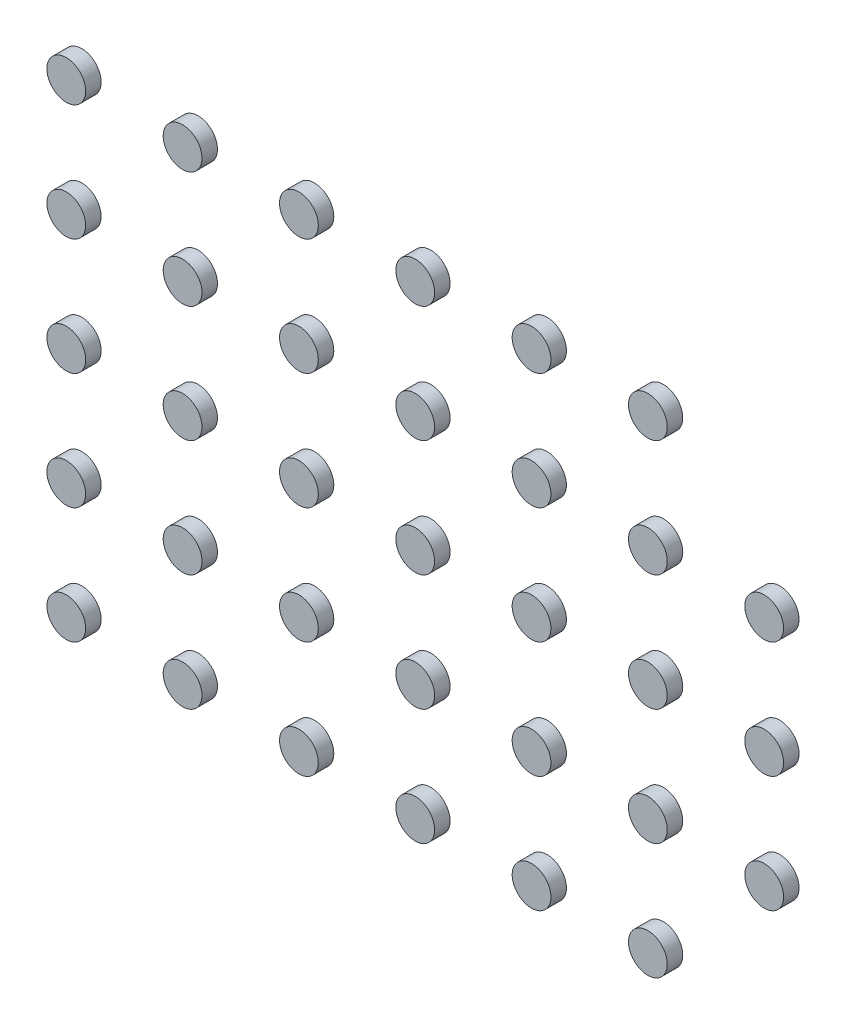
SolidWorks part; units mm, degrees
ref_plane "前视基准面" through (0, 0, 0) normal (0, 0, 1) x (1, 0, 0)
ref_plane "上视基准面" through (0, 0, 0) normal (0, 1, 0) x (1, 0, 0)
ref_plane "右视基准面" through (0, 0, 0) normal (1, 0, 0) x (0, 0, -1)
other "Configuration Table"
sketch "草图1" plane through (0, 0, 0) normal (0, 0, 1) x (1, 0, 0)
  circle A0 centre (-10.5, -7.5) radius 0.5
  circle A1 centre (-10.5, -4.5) radius 0.5
  circle A2 centre (-10.5, -1.5) radius 0.5
  circle A3 centre (-10.5, 4.5) radius 0.5
  circle A4 centre (-7.5, 4.5) radius 0.5
  circle A5 centre (-7.5, -1.5) radius 0.5
  circle A6 centre (-7.5, -4.5) radius 0.5
  circle A7 centre (-7.5, -7.5) radius 0.5
  circle A8 centre (-4.5, -7.5) radius 0.5
  circle A9 centre (-4.5, -4.5) radius 0.5
  circle A10 centre (-4.5, 1.5) radius 0.5
  circle A11 centre (-4.5, 4.5) radius 0.5
  circle A12 centre (-1.5, 4.5) radius 0.5
  circle A13 centre (-1.5, 1.5) radius 0.5
  circle A14 centre (1.5, -1.5) radius 0.5
  circle A15 centre (-1.5, -1.5) radius 0.5
  circle A16 centre (-1.5, -4.5) radius 0.5
  circle A17 centre (-1.5, -7.5) radius 0.5
  circle A18 centre (1.5, -7.5) radius 0.5
  circle A19 centre (1.5, -4.5) radius 0.5
  circle A20 centre (1.5, 1.5) radius 0.5
  circle A21 centre (1.5, 4.5) radius 0.5
  circle A22 centre (4.5, 4.5) radius 0.5
  circle A23 centre (4.5, 1.5) radius 0.5
  circle A24 centre (4.5, -1.5) radius 0.5
  circle A25 centre (4.5, -4.5) radius 0.5
  circle A26 centre (4.5, -7.5) radius 0.5
  circle A27 centre (7.5, -4.5) radius 0.5
  circle A28 centre (7.5, 1.5) radius 0.5
  circle A29 centre (7.5, -1.5) radius 0.5
  circle A30 centre (10.5, -1.5) radius 0.5
  circle A31 centre (10.5, 1.5) radius 0.5
  circle A32 centre (7.5, 4.5) radius 0.5
  circle A33 centre (4.5, 7.5) radius 0.5
  circle A34 centre (1.5, 7.5) radius 0.5
  circle A35 centre (-1.5, 7.5) radius 0.5
  circle A36 centre (-4.5, 7.5) radius 0.5
  circle A37 centre (-7.5, 7.5) radius 0.5
  circle A38 centre (-10.5, 7.5) radius 0.5
  circle A39 centre (-4.5, -1.5) radius 0.5
  circle A40 centre (-1.5, -1.5) radius 0.5
  circle A41 centre (-7.5, 1.5) radius 0.5
  circle A42 centre (-10.5, 1.5) radius 0.5
extrude "凸台-拉伸1" add sketch "草图1" along normal blind 0.4 contours A10 | A13 | A20 | A23 | A28 | A31 | A30 | A29 | A38 | A35 | A34 | A33 | A42 | A3 | A2 | A1 | A0 | A7 | A6 | A5 | A41 | A4 | A11 | A12 | A21 | A32 | A14 | A15 | A39 | A9 | A16 | A8 | A17 | A18 | A26 | A25 | A27 | A24 | A37 | A36 | A22 | A19
delete or keep bodies "实体-删除/保留 1" type keep bodies bodies 140 134 128 122 139 133 110 127 121 138 132 109 126 143 120 137 108 125 142 119 136 113 130 107 124 141 118 147 135 129 146 106 123
